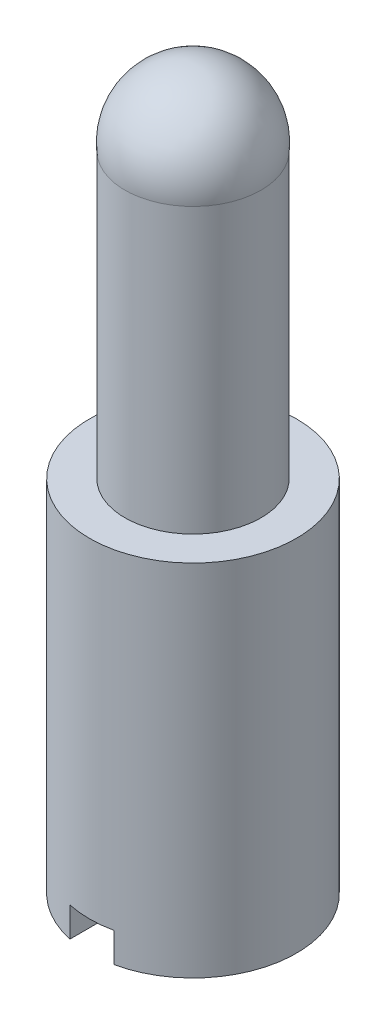
SolidWorks part; units mm, degrees
ref_plane "Front Plane" through (0, 0, 0) normal (0, 0, 1) x (1, 0, 0)
ref_plane "Top Plane" through (0, 0, 0) normal (0, 1, 0) x (1, 0, 0)
ref_plane "Right Plane" through (0, 0, 0) normal (1, 0, 0) x (0, 0, -1)
sketch "Sketch1" plane through (0, 0, 0) normal (0, 0, 1) x (1, 0, 0)
  line L0 (0, 0) -> (0, 19.05)
  line L1 (0, 0) -> (2.7432, 0)
  line L2 (2.7432, 0) -> (2.7432, 9.525)
  line L3 (2.7432, 9.525) -> (1.8034, 9.525)
  line L4 (1.8034, 9.525) -> (1.8034, 17.0458)
  arc A0 (1.8034, 17.0458) -> (0, 19.05) centre (0, 17.2365) ccw
  point P8 (0, 0)
  dimension "D1" = 19.05
  dimension "D2" = 9.525
  dimension "D3" = 2.7432
  dimension "D4" = 1.8034
revolve "Revolve1" add sketch "Sketch1" angle 360 about L0
cosmetic thread "Cosmetic Thread1" parameters "D2"=4.2266
sketch "Sketch2" plane through (0, 0, 0) normal (0, 0, 1) x (1, 0, 0)
  line L0 (-2.7432, 0) -> (2.7432, 0) construction
  line L1 (-0.5842, 0) -> (0.5842, 0)
  line L2 (-0.5842, 0) -> (-0.5842, 0.7874)
  line L3 (-0.5842, 0.7874) -> (0.5842, 0.7874)
  line L4 (0.5842, 0) -> (0.5842, 0.7874)
  dimension "D1" = 0.7874
  dimension "D2" = 1.1684
extrude "Cut-Extrude1" cut sketch "Sketch2" against normal through all both and the other way through all
